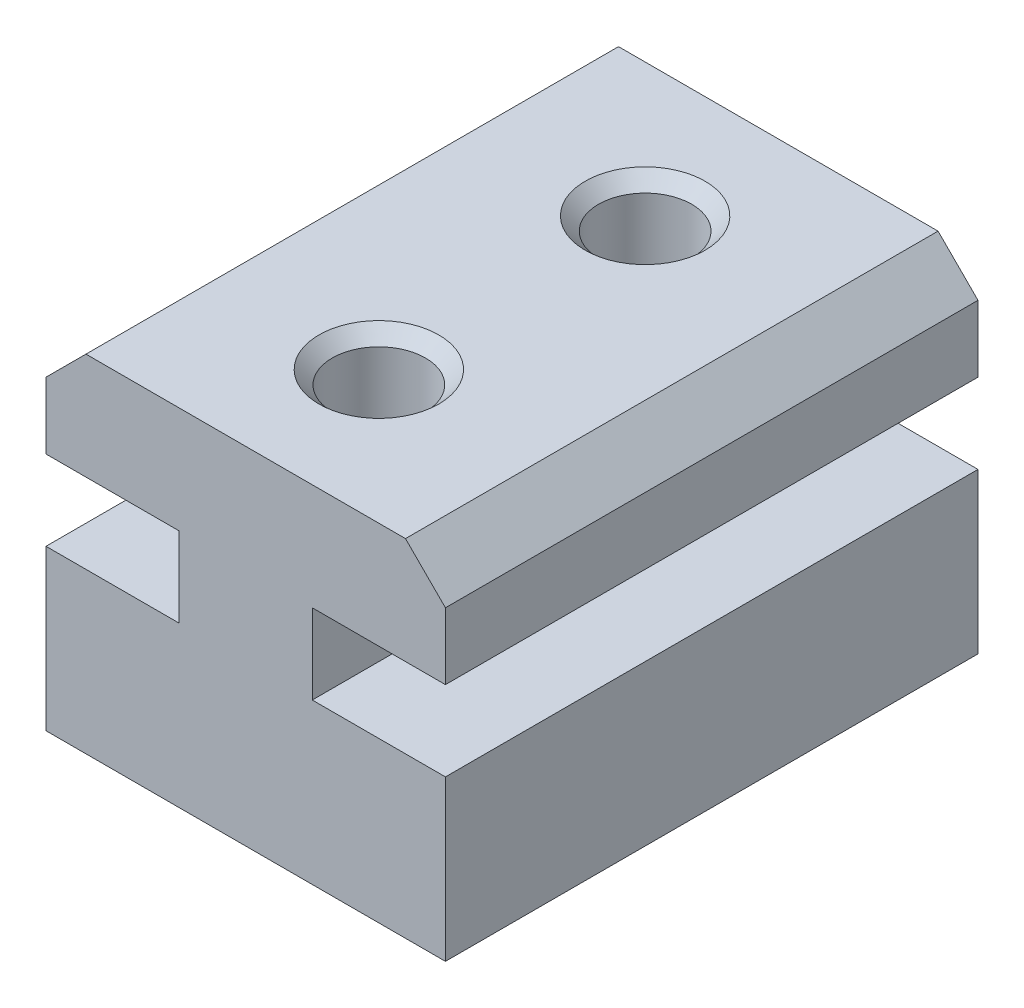
SolidWorks part; units mm, degrees
ref_plane "Front Plane" through (0, 0, 0) normal (0, 0, 1) x (1, 0, 0)
ref_plane "Top Plane" through (0, 0, 0) normal (0, 1, 0) x (1, 0, 0)
ref_plane "Right Plane" through (0, 0, 0) normal (1, 0, 0) x (0, 0, -1)
sketch "Sketch1" plane through (0, 0, 0) normal (0, 0, 1) x (1, 0, 0)
  line L0 (0, 0) -> (15, 0)
  line L5 (15, 0) -> (15, 6)
  line L6 (15, 6) -> (10, 6)
  line L11 (10, 6) -> (10, 9)
  line L12 (10, 9) -> (15, 9)
  line L17 (15, 9) -> (15, 13)
  line L18 (15, 13) -> (0, 13)
  line L19 (0, 13) -> (0, 9)
  line L20 (0, 9) -> (5, 9)
  line L21 (5, 9) -> (5, 6)
  line L22 (5, 6) -> (0, 6)
  line L23 (0, 6) -> (0, 0)
  line L24 (5, 6) -> (10, 6) construction
  line L25 (10, 9) -> (5, 9) construction
  line L26 (0, 9) -> (0, 6) construction
  line L27 (15, 6) -> (15, 9) construction
  point P3 (5, 7.5)
  dimension "D1" = 6
  dimension "D2" = 3
  dimension "D3" = 4
  dimension "D4" = 5
  dimension "D5" = 5
extrude "Boss-Extrude1" add sketch "Sketch1" along normal mid plane 20
sketch "Sketch2" plane through (0, 13, 0) normal (0, 1, 0) x (1, 0, 0)
  line L0 (7.5, -10) -> (7.5, -5) construction
  line L1 (7.5, -5) -> (7.5, 0) construction
  line L2 (7.5, 0) -> (7.5, 5) construction
  line L3 (7.5, 5) -> (7.5, 10) construction
  line L4 (15, 10) -> (0, 10)
  line L5 (0, 10) -> (0, -10)
  line L6 (0, -10) -> (15, -10)
  line L7 (15, -10) -> (15, 10)
  line L8 (15, 10) -> (0, 10)
  line L9 (0, 10) -> (0, -10)
  line L10 (0, -10) -> (15, -10)
  line L11 (15, -10) -> (15, 10)
  line L12 (0, 0) -> (7.5, 0) construction
  circle A0 centre (7.5, 5) radius 1.75
  circle A1 centre (7.5, -5) radius 1.75
  point P13 (0, 0)
  dimension "D2" = 3.5
  dimension "D1" = 0
extrude "Cut-Extrude1" cut sketch "Sketch2" against normal through all contours A1 | A0
chamfer "Chamfer1" distance 1.5 angle 45 2 edges at (0, 13, 0) (15, 13, 0)
chamfer "Chamfer3" distance 0.5 angle 45 2 edges at (5.75, 13, -5) (5.75, 13, 5)
